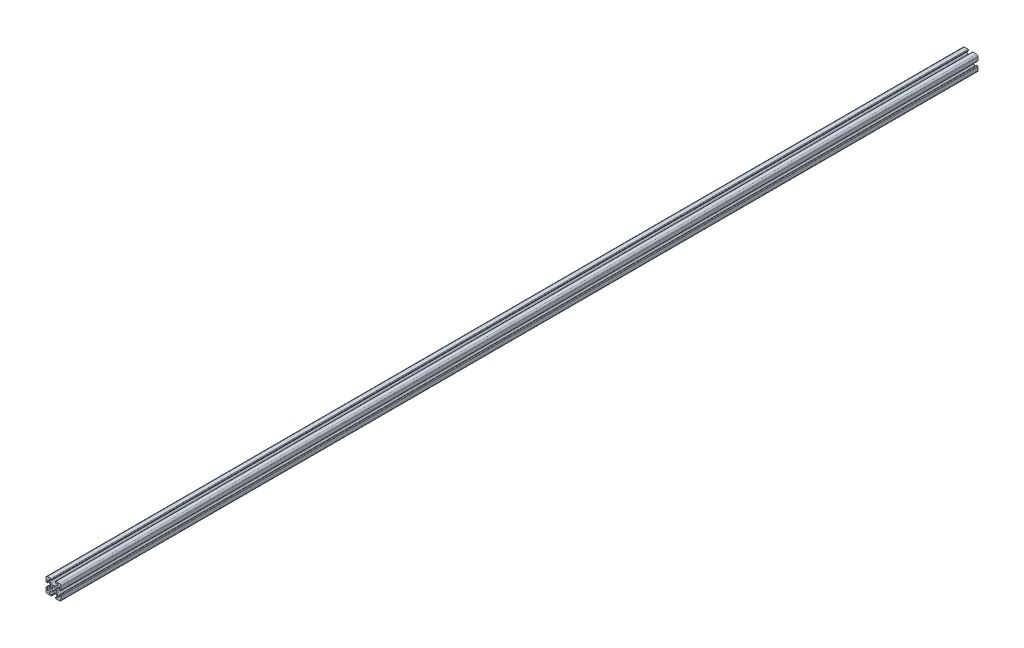
SolidWorks part; units mm, degrees
ref_plane "Front Plane" through (0, 0, 0) normal (0, 0, 1) x (1, 0, 0)
ref_plane "Top Plane" through (0, 0, 0) normal (0, 1, 0) x (1, 0, 0)
ref_plane "Right Plane" through (0, 0, 0) normal (1, 0, 0) x (0, 0, -1)
sketch "Sketch1" plane through (0, 0, 0) normal (0, 0, 1) x (1, 0, 0)
  line L0 (0, 10) -> (0, -10) construction
  line L1 (10, 0) -> (-10, 0) construction
  line L2 (-2.5, 10) -> (2.5, 10) construction
  line L3 (-5.75, 8.2) -> (5.75, 8.2) construction
  circle A0 centre (0, 0) radius 2.15 construction
  point P4 (0, 0)
  point P8 (0, 0)
  point P10 (0, 3.6)
  point P14 (0, 10)
  point P17 (0, 8.2)
  dimension "Thru Hole" = 4.3
  dimension "Height" = 20
  dimension "T Slot Depth" = 6.4
  dimension "T Slot Top Width" = 5
  dimension "T Slot Max Width" = 11.5
  dimension "Wall" = 1.8
sketch "Sketch2" plane through (0, 0, 0) normal (1, 0, 0) x (0, 0, -1)
  line L0 (610, 0) -> (-610, 0) construction
  point P4 (0, 0)
  dimension "D1" = 1220
sketch "Sketch3" plane through (0, 0, 0) normal (0, 0, 1) x (1, 0, 0)
  line L0 (3.2874, 10) -> (8, 10)
  line L1 (10, 8) -> (10, -8) construction
  line L2 (8, -10) -> (-8, -10) construction
  line L3 (-10, 10) -> (10, -10) construction
  line L4 (2.5, 9.2126) -> (2.5, 8.5048)
  line L5 (-5.75, 8.2) -> (5.75, 8.2) construction
  line L6 (2.8048, 8.2) -> (4.9118, 8.2)
  line L7 (5.5045, 6.7691) -> (3.2141, 4.4787)
  line L8 (1.0928, 3.6) -> (-1.0928, 3.6)
  line L9 (0, 10) -> (0, -10) construction
  line L10 (5.75, 8.2) -> (5.75, 0) construction
  line L11 (10, 0) -> (-10, 0) construction
  line L12 (0, 0) -> (0, 10) construction
  line L13 (-2.5, 9.2126) -> (-2.5, 8.5048)
  line L14 (-5.5045, 6.7691) -> (-3.2141, 4.4787)
  line L15 (-2.8048, 8.2) -> (-4.9118, 8.2)
  line L16 (-3.2874, 10) -> (-8, 10)
  line L17 (0, 0) -> (-10, 0) construction
  line L18 (-10, 3.2874) -> (-10, 8)
  line L19 (-8.2, 2.8048) -> (-8.2, 4.9118)
  line L20 (-6.7691, 5.5045) -> (-4.4787, 3.2141)
  line L21 (-9.2126, 2.5) -> (-8.5048, 2.5)
  line L22 (-3.6, -1.0928) -> (-3.6, 1.0928)
  line L23 (-6.7691, -5.5045) -> (-4.4787, -3.2141)
  line L24 (-8.2, -2.8048) -> (-8.2, -4.9118)
  line L25 (-9.2126, -2.5) -> (-8.5048, -2.5)
  line L26 (-10, -3.2874) -> (-10, -8)
  line L27 (9.2126, -2.5) -> (8.5048, -2.5)
  line L28 (8.2, -2.8048) -> (8.2, -4.9118)
  line L29 (6.7691, -5.5045) -> (4.4787, -3.2141)
  line L30 (3.6, -1.0928) -> (3.6, 1.0928)
  line L31 (9.2126, 2.5) -> (8.5048, 2.5)
  line L32 (6.7691, 5.5045) -> (4.4787, 3.2141)
  line L33 (8.2, 2.8048) -> (8.2, 4.9118)
  line L34 (10, 8) -> (10, 3.2874)
  line L35 (10, -3.2874) -> (10, -8)
  line L36 (3.2874, -10) -> (8, -10)
  line L37 (-3.2874, -10) -> (-8, -10)
  line L38 (-6.7691, -5.5045) -> (-4.4787, -3.2141)
  line L39 (-2.8048, -8.2) -> (-4.9118, -8.2)
  line L40 (-5.5045, -6.7691) -> (-3.2141, -4.4787)
  line L41 (-2.5, -9.2126) -> (-2.5, -8.5048)
  line L42 (1.0928, -3.6) -> (-1.0928, -3.6)
  line L43 (5.5045, -6.7691) -> (3.2141, -4.4787)
  line L44 (2.8048, -8.2) -> (4.9118, -8.2)
  line L45 (2.5, -9.2126) -> (2.5, -8.5048)
  arc A0 (4.9118, 8.2) -> (5.5045, 6.7691) centre (4.9118, 7.3618) cw
  arc A1 (3.2141, 4.4787) -> (1.0928, 3.6) centre (1.0928, 6.6) cw
  circle A2 centre (0, 0) radius 2.15 construction
  circle A3 centre (0, 0) radius 2.15
  arc A4 (3.2874, 10) -> (2.5, 9.2126) centre (3.2874, 9.2126) ccw
  arc A5 (2.5, 8.5048) -> (2.8048, 8.2) centre (2.8048, 8.5048) ccw
  arc A6 (-3.2874, 10) -> (-2.5, 9.2126) centre (-3.2874, 9.2126) cw
  arc A7 (-4.9118, 8.2) -> (-5.5045, 6.7691) centre (-4.9118, 7.3618) ccw
  arc A8 (-3.2141, 4.4787) -> (-1.0928, 3.6) centre (-1.0928, 6.6) ccw
  arc A9 (-2.5, 8.5048) -> (-2.8048, 8.2) centre (-2.8048, 8.5048) cw
  arc A10 (-8.5048, 2.5) -> (-8.2, 2.8048) centre (-8.5048, 2.8048) ccw
  arc A11 (-4.4787, 3.2141) -> (-3.6, 1.0928) centre (-6.6, 1.0928) cw
  arc A12 (-8.2, 4.9118) -> (-6.7691, 5.5045) centre (-7.3618, 4.9118) cw
  arc A13 (-10, 3.2874) -> (-9.2126, 2.5) centre (-9.2126, 3.2874) ccw
  arc A14 (-8.5048, -2.5) -> (-8.2, -2.8048) centre (-8.5048, -2.8048) cw
  arc A15 (-10, -3.2874) -> (-9.2126, -2.5) centre (-9.2126, -3.2874) cw
  arc A16 (-4.4787, -3.2141) -> (-3.6, -1.0928) centre (-6.6, -1.0928) ccw
  arc A17 (-8.2, -4.9118) -> (-6.7691, -5.5045) centre (-7.3618, -4.9118) ccw
  arc A26 (-8, -10) -> (-10, -8) centre (-8, -8) cw
  arc A27 (-8, 10) -> (-10, 8) centre (-8, 8) ccw
  arc A28 (8, 10) -> (10, 8) centre (8, 8) cw
  arc A29 (10, -8) -> (8, -10) centre (8, -8) cw
  arc A30 (8.2, -4.9118) -> (6.7691, -5.5045) centre (7.3618, -4.9118) cw
  arc A31 (4.4787, -3.2141) -> (3.6, -1.0928) centre (6.6, -1.0928) cw
  arc A32 (10, -3.2874) -> (9.2126, -2.5) centre (9.2126, -3.2874) ccw
  arc A33 (8.5048, -2.5) -> (8.2, -2.8048) centre (8.5048, -2.8048) ccw
  arc A34 (10, 3.2874) -> (9.2126, 2.5) centre (9.2126, 3.2874) cw
  arc A35 (8.2, 4.9118) -> (6.7691, 5.5045) centre (7.3618, 4.9118) ccw
  arc A36 (4.4787, 3.2141) -> (3.6, 1.0928) centre (6.6, 1.0928) ccw
  arc A37 (8.5048, 2.5) -> (8.2, 2.8048) centre (8.5048, 2.8048) cw
  arc A38 (-2.5, -8.5048) -> (-2.8048, -8.2) centre (-2.8048, -8.5048) ccw
  arc A39 (-3.2141, -4.4787) -> (-1.0928, -3.6) centre (-1.0928, -6.6) cw
  arc A40 (-4.9118, -8.2) -> (-5.5045, -6.7691) centre (-4.9118, -7.3618) cw
  arc A41 (-3.2874, -10) -> (-2.5, -9.2126) centre (-3.2874, -9.2126) ccw
  arc A42 (2.5, -8.5048) -> (2.8048, -8.2) centre (2.8048, -8.5048) cw
  arc A43 (3.2874, -10) -> (2.5, -9.2126) centre (3.2874, -9.2126) cw
  arc A44 (3.2141, -4.4787) -> (1.0928, -3.6) centre (1.0928, -6.6) ccw
  arc A45 (4.9118, -8.2) -> (5.5045, -6.7691) centre (4.9118, -7.3618) ccw
  point P36 (2.5, 10)
  point P39 (2.5, 8.2)
  point P49 (0, 3.6)
  point P77 (-3.6, 0)
  point P78 (-8.2, -2.5)
  point P79 (-10, -2.5)
  point P104 (-10, -10)
  point P110 (10, 10)
  point P114 (10, -2.5)
  point P115 (8.2, -2.5)
  point P116 (3.6, 0)
  point P141 (0, -3.6)
  dimension "D1" = 3
  dimension "D2" = 0.8382
  dimension "D4" = 0.7874
  dimension "D5" = 0.3048
  dimension "D6" = 2
  dimension "D3" = 45
extrude "Boss-Extrude1" add sketch "Sketch3" along normal up to vertex (610 mm away) and the other way up to vertex (610 mm away) contours A45 L44 A42 L45 A43 L36 A29 L35 A32 L27 A33 L28 A30 L29 A31 L30 A36 L32 A35 L33 A37 L31 A34 L34 A28 L0 A4 L4 A5 L6 A0 L7 A1 L8 A8 L14 A7 L15 A9 L13 A6 L16 A27 L18 A13 L21 A10 L19 A12 L20 A11 up to point (0, 0, 610) other way up to point (0, 0, -610)
